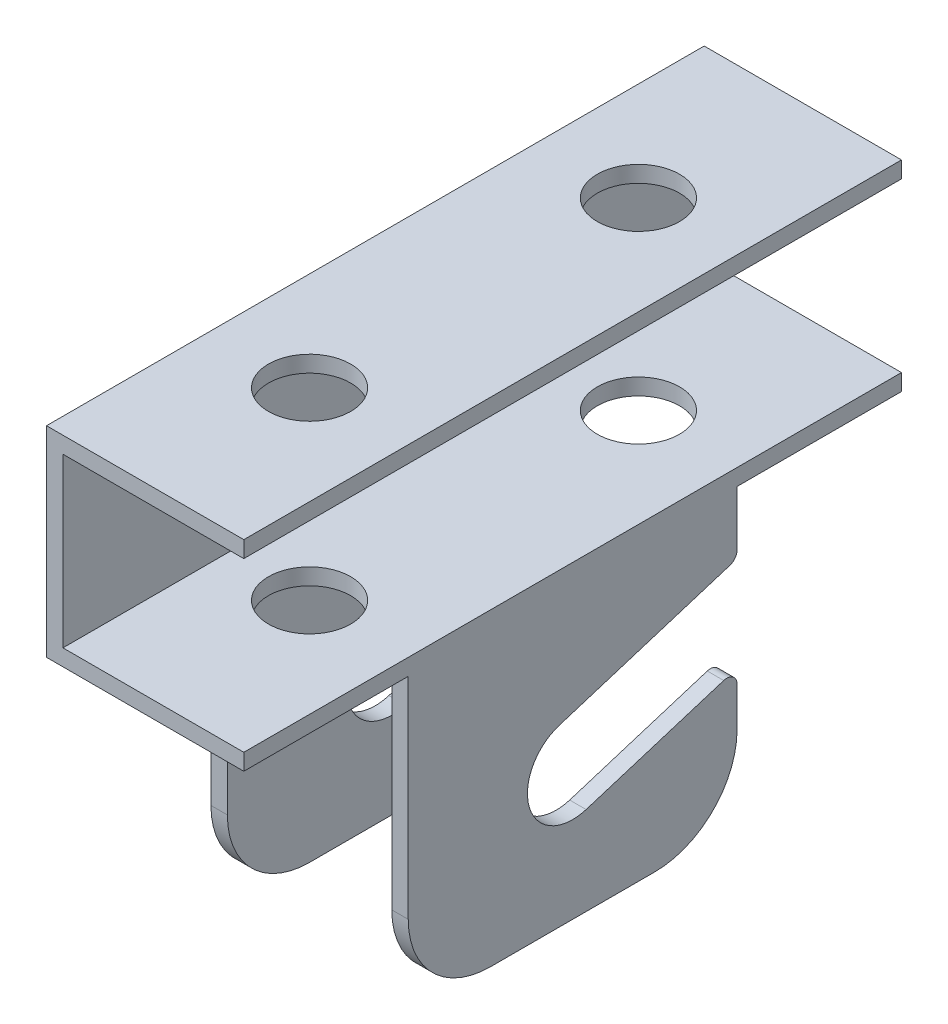
SolidWorks part; units mm, degrees
material "AISI 1015 Steel, Cold Drawn (SS)"
ref_plane "Front Plane" through (0, 0, 0) normal (0, 0, 1) x (1, 0, 0)
ref_plane "Top Plane" through (0, 0, 0) normal (0, 1, 0) x (1, 0, 0)
ref_plane "Right Plane" through (0, 0, 0) normal (1, 0, 0) x (0, 0, -1)
other "Configuration Table"
sketch "Sketch1" plane through (0, 0, 0) normal (0, 0, 1) x (1, 0, 0)
  line L0 (0, 0) -> (0, 76.2)
  line L1 (0, 76.2) -> (30.48, 76.2)
  line L2 (30.48, 76.2) -> (30.48, 73.66)
  line L3 (30.48, 73.66) -> (2.54, 73.66)
  line L4 (2.54, 73.66) -> (2.54, 47.752)
  line L5 (2.54, 47.752) -> (30.48, 47.752)
  line L6 (30.48, 47.752) -> (30.48, 0)
  line L7 (30.48, 0) -> (27.94, 0)
  line L8 (27.94, 0) -> (27.94, 45.212)
  line L9 (27.94, 45.212) -> (2.54, 45.212)
  line L10 (2.54, 45.212) -> (2.54, 0)
  line L11 (2.54, 0) -> (0, 0)
  point P13 (30.48, 74.93)
  dimension "D1" = 76.2
  dimension "D2" = 30.48
  dimension "D3" = 2.54
  dimension "D4" = 2.54
  dimension "D5" = 2.54
  dimension "D6" = 25.908
extrude "Boss-Extrude1" add sketch "Sketch1" along normal mid plane 101.6
sketch "Sketch4" plane through (30.48, 0, 0) normal (1, 0, 0) x (0, 0, -1)
  line L0 (-50.8, 0) -> (50.8, 0) construction
  line L1 (-50.8, 45.212) -> (-25.4, 45.212)
  line L2 (-50.8, 45.212) -> (-50.8, 0)
  line L3 (-50.8, 0) -> (-25.4, 0)
  line L4 (-25.4, 45.212) -> (-25.4, 0)
  line L6 (50.8, 45.212) -> (25.4, 45.212)
  line L7 (50.8, 45.212) -> (50.8, 0)
  line L8 (50.8, 0) -> (25.4, 0)
  line L9 (25.4, 45.212) -> (25.4, 0)
  dimension "D1" = 25.4
  dimension "D2" = 25.4
extrude "Cut-Extrude1" cut sketch "Sketch4" against normal through all both and the other way through all
sketch "Sketch5" plane through (0, 0, 0) normal (-1, 0, 0) x (0, 0, 1)
  line L0 (25.4, 0) -> (-25.4, 0) construction
  line L1 (2.08, 26.9881) -> (-25.4, 35.56)
  line L2 (-2.08, 13.6519) -> (-25.4, 20.9261)
  line L3 (-25.4, 45.212) -> (-25.4, 0) construction
  line L4 (-50.8, 45.212) -> (-25.4, 45.212) construction
  line L5 (-25.4, 35.56) -> (-25.4, 20.9261)
  arc A0 (-2.08, 13.6519) -> (2.08, 26.9881) centre (0, 20.32) ccw
  dimension "D2" = 13.97
  dimension "D1" = 20.32
  dimension "D3" = 9.652
  dimension "D4" = 25.4
extrude "Cut-Extrude2" cut sketch "Sketch5" against normal through all both
fillet "Fillet1" radius 12.7 4 edges at (29.21, 0, 25.4) (1.27, 0, 25.4) (29.21, 0, -25.4) (1.27, 0, -25.4)
fillet "Fillet2" radius 1.5875 4 edges at (29.21, 20.9261, -25.4) (29.21, 35.56, -25.4) (1.27, 35.56, -25.4) (1.27, 20.9261, -25.4)
sketch "Sketch6" plane through (0, 76.2, 0) normal (0, 1, 0) x (1, 0, 0)
  line L0 (2.54, -50.8) -> (2.54, 50.8) construction
  line L1 (30.48, 50.8) -> (0, 50.8) construction
  circle A0 centre (15.24, 25.4) radius 6.35
  circle A1 centre (15.24, -25.4) radius 6.35
  dimension "D5" = 12.7
  dimension "D1" = 12.7
  dimension "D2" = 25.4
  dimension "D3" = 50.8
  dimension "D4" = 12.7
extrude "BOLT HOLES" cut sketch "Sketch6" against normal blind 50.8 and the other way through all
equation "\"A\"= 3"
equation "\"B\"= 1"
